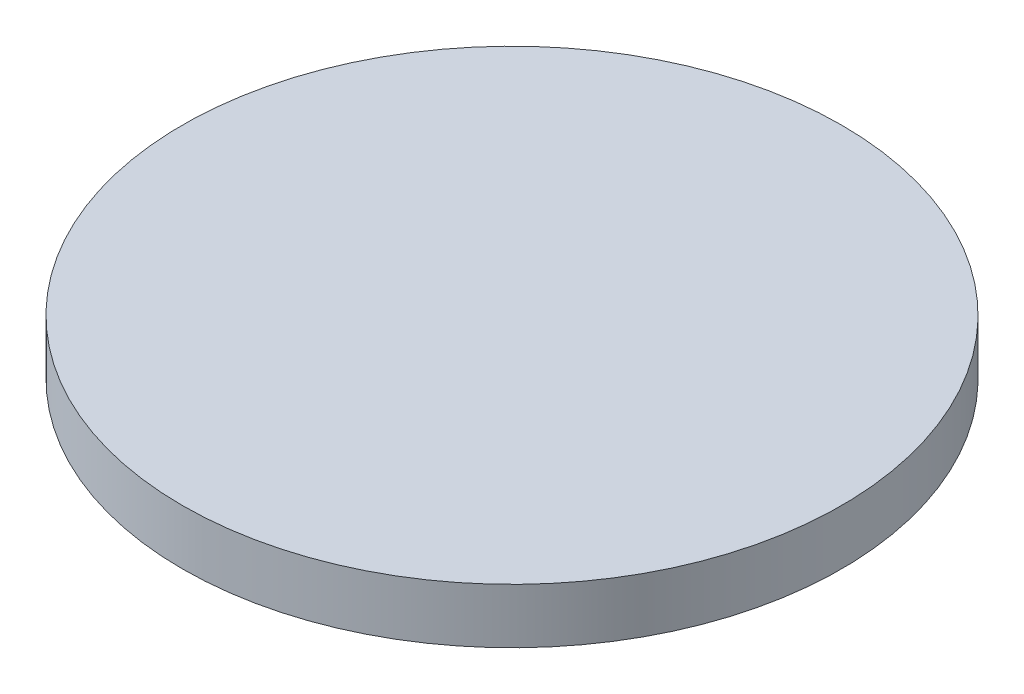
SolidWorks part; units mm, degrees
ref_plane "Front Plane" through (0, 0, 0) normal (0, 0, 1) x (1, 0, 0)
ref_plane "Top Plane" through (0, 0, 0) normal (0, 1, 0) x (1, 0, 0)
ref_plane "Right Plane" through (0, 0, 0) normal (1, 0, 0) x (0, 0, -1)
sketch "Sketch1" plane through (0, 0, 0) normal (0, 1, 0) x (1, 0, 0)
  circle A0 centre (0, 0) radius 60
extrude "Boss-Extrude1" add sketch "Sketch1" along normal blind 10
sketch "Sketch2" plane through (0, 0, 0) normal (0, -1, 0) x (1, 0, 0)
  circle A0 centre (0, 0) radius 1.5
extrude "Cut-Extrude1" cut sketch "Sketch2" against normal blind 4
